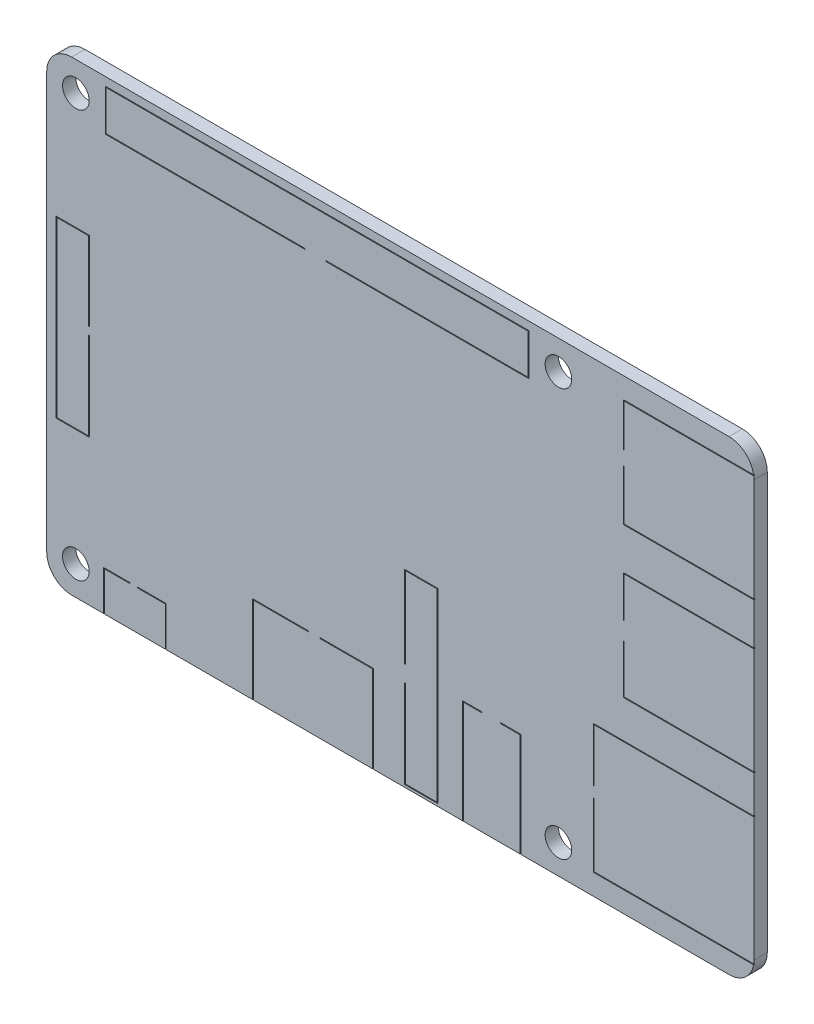
SolidWorks part; units mm, degrees
ref_plane "Front Plane" through (0, 0, 0) normal (0, 0, 1) x (1, 0, 0)
ref_plane "Top Plane" through (0, 0, 0) normal (0, 1, 0) x (1, 0, 0)
ref_plane "Right Plane" through (0, 0, 0) normal (1, 0, 0) x (0, 0, -1)
sketch "Sketch1" plane through (0, 0, 0) normal (0, 0, 1) x (1, 0, 0)
  line L1 (-39.5, -28) -> (39.5, -28)
  line L2 (-42.5, -25) -> (-42.5, 25)
  line L3 (-39.5, 28) -> (39.5, 28)
  line L4 (42.5, -25) -> (42.5, 25)
  line L5 (-42.5, -28) -> (42.5, 28) construction
  line L6 (-42.5, 28) -> (42.5, -28) construction
  arc A0 (-39.5, -28) -> (-42.5, -25) centre (-39.5, -25) cw
  arc A1 (39.5, -28) -> (42.5, -25) centre (39.5, -25) ccw
  arc A2 (39.5, 28) -> (42.5, 25) centre (39.5, 25) cw
  arc A3 (-42.5, 25) -> (-39.5, 28) centre (-39.5, 25) cw
  circle A4 centre (-39, 24.5) radius 1.6
  circle A5 centre (-39, -24.5) radius 1.6
  circle A6 centre (19, 24.5) radius 1.6
  circle A7 centre (19, -24.5) radius 1.6
  point P0 (0, 0)
  dimension "D3" = 3
  dimension "D4" = 3.2
  dimension "D5" = 3.5
  dimension "D6" = 3.5
  dimension "D7" = 58
  dimension "D8" = 58
  dimension "D9" = 49
  dimension "D12" = 49
  dimension "D1" = 85
  dimension "D2" = 56
  dimension "D10" = 24.5
  dimension "D11" = 24.5
extrude "Boss-Extrude1" add sketch "Sketch1" along normal blind 1.6
sketch "Sketch2" plane through (0, 0, 1.6) normal (0, 0, 1) x (1, 0, 0)
  line L1 (-42.5, 25) -> (-42.5, -25) construction
  line L2 (-35.65, -28.6369) -> (-28.15, -28.6369)
  line L3 (-35.65, -28.6369) -> (-35.65, -23.2)
  line L4 (-35.65, -23.2) -> (-32.465, -23.2)
  line L5 (-28.15, -28.6369) -> (-28.15, -23.2)
  line L6 (-35.65, -28.6369) -> (-28.15, -23.2) construction
  line L7 (-35.65, -23.2) -> (-28.15, -28.6369) construction
  line L8 (-39.5, -28) -> (39.5, -28) construction
  line L9 (-17.75, -17.5) -> (-11.0158, -17.5)
  line L10 (-17.75, -17.5) -> (-17.75, -33.1614)
  line L11 (-17.75, -33.1614) -> (-3.25, -33.1614)
  line L12 (-3.25, -17.5) -> (-3.25, -33.1614)
  line L13 (-17.75, -17.5) -> (-3.25, -33.1614) construction
  line L14 (-17.75, -33.1614) -> (-3.25, -17.5) construction
  line L15 (0.5, -5.3) -> (4.5, -5.3)
  line L16 (0.5, -5.3) -> (0.5, -15.174)
  line L17 (0.5, -27.7) -> (4.5, -27.7)
  line L18 (4.5, -5.3) -> (4.5, -27.7)
  line L19 (0.5, -5.3) -> (4.5, -27.7) construction
  line L20 (0.5, -27.7) -> (4.5, -5.3) construction
  line L21 (7.5, -15.5) -> (9.7992, -15.5)
  line L22 (7.5, -15.5) -> (7.5, -31.1614)
  line L23 (7.5, -31.1614) -> (14.5, -31.1614)
  line L24 (14.5, -15.5) -> (14.5, -31.1614)
  line L25 (7.5, -15.5) -> (14.5, -31.1614) construction
  line L26 (7.5, -31.1614) -> (14.5, -15.5) construction
  line L27 (-35.45, 27) -> (15.45, 27)
  line L28 (-35.45, 27) -> (-35.45, 22)
  line L29 (-35.45, 22) -> (-11.4582, 22)
  line L30 (15.45, 27) -> (15.45, 22)
  line L31 (-35.45, 27) -> (15.45, 22) construction
  line L32 (-35.45, 22) -> (15.45, 27) construction
  line L33 (-41.3717, -10.5142) -> (-37.3717, -10.5142)
  line L34 (-41.3717, -10.5142) -> (-41.3717, 10.5142)
  line L35 (-41.3717, 10.5142) -> (-37.3717, 10.5142)
  line L36 (-37.3717, -10.5142) -> (-37.3717, 0.0947)
  line L37 (-41.3717, -10.5142) -> (-37.3717, 10.5142) construction
  line L38 (-41.3717, 10.5142) -> (-37.3717, -10.5142) construction
  line L39 (42.5, -25) -> (42.5, 25) construction
  line L40 (23.2, -25.5) -> (44.7, -25.5)
  line L41 (23.2, -25.5) -> (23.2, -17.75)
  line L42 (23.2, -10) -> (44.7, -10)
  line L43 (44.7, -25.5) -> (44.7, -10)
  line L44 (23.2, -25.5) -> (44.7, -10) construction
  line L45 (23.2, -10) -> (44.7, -25.5) construction
  line L46 (26.8, -5.5) -> (54.0714, -5.5)
  line L47 (26.8, -5.5) -> (26.8, 0.4072)
  line L48 (26.8, 7.5) -> (54.0714, 7.5)
  line L49 (54.0714, -5.5) -> (54.0714, 7.5)
  line L50 (26.8, -5.5) -> (54.0714, 7.5) construction
  line L51 (26.8, 7.5) -> (54.0714, -5.5) construction
  line L52 (26.8, 12.5) -> (57.7137, 12.5)
  line L53 (26.8, 12.5) -> (26.8, 18.6113)
  line L54 (26.8, 25.5) -> (57.7137, 25.5)
  line L55 (57.7137, 12.5) -> (57.7137, 25.5)
  line L56 (26.8, 12.5) -> (57.7137, 25.5) construction
  line L57 (26.8, 25.5) -> (57.7137, 12.5) construction
  line L58 (-35.35, 22.1) -> (-11.4582, 22.1)
  line L59 (15.35, 26.9) -> (15.35, 22.1)
  line L60 (-35.35, 26.9) -> (15.35, 26.9)
  line L61 (-35.35, 26.9) -> (-35.35, 22.1)
  line L62 (-41.2717, 10.4142) -> (-37.4717, 10.4142)
  line L63 (-37.4717, -10.4142) -> (-37.4717, 0.0947)
  line L64 (-41.2717, -10.4142) -> (-37.4717, -10.4142)
  line L65 (-41.2717, -10.4142) -> (-41.2717, 10.4142)
  line L66 (-35.55, -28.5369) -> (-35.55, -23.3)
  line L67 (-35.55, -23.3) -> (-32.465, -23.3)
  line L68 (-28.25, -28.5369) -> (-28.25, -23.3)
  line L69 (-35.55, -28.5369) -> (-28.25, -28.5369)
  line L70 (-17.65, -17.6) -> (-17.65, -33.0614)
  line L71 (-17.65, -33.0614) -> (-3.35, -33.0614)
  line L72 (-3.35, -17.6) -> (-3.35, -33.0614)
  line L73 (-17.65, -17.6) -> (-11.0158, -17.6)
  line L74 (0.6, -5.4) -> (0.6, -15.174)
  line L75 (0.6, -27.6) -> (4.4, -27.6)
  line L76 (4.4, -5.4) -> (4.4, -27.6)
  line L77 (0.6, -5.4) -> (4.4, -5.4)
  line L78 (7.6, -15.6) -> (9.7992, -15.6)
  line L79 (14.4, -15.6) -> (14.4, -31.0614)
  line L80 (7.6, -31.0614) -> (14.4, -31.0614)
  line L81 (7.6, -15.6) -> (7.6, -31.0614)
  line L82 (23.3, -25.4) -> (23.3, -17.75)
  line L83 (23.3, -10.1) -> (44.6, -10.1)
  line L84 (44.6, -25.4) -> (44.6, -10.1)
  line L85 (23.3, -25.4) -> (44.6, -25.4)
  line L86 (26.9, -5.4) -> (53.9714, -5.4)
  line L87 (53.9714, -5.4) -> (53.9714, 7.4)
  line L88 (26.9, 7.4) -> (53.9714, 7.4)
  line L89 (26.9, -5.4) -> (26.9, 0.4072)
  line L90 (26.9, 12.6) -> (57.6137, 12.6)
  line L91 (57.6137, 12.6) -> (57.6137, 25.4)
  line L92 (26.9, 25.4) -> (57.6137, 25.4)
  line L93 (26.9, 12.6) -> (26.9, 18.6113)
  line L94 (-37.4717, 1) -> (-37.4717, 10.4142)
  line L95 (-37.4717, 1) -> (-37.3717, 1)
  line L96 (26.9, 20.2773) -> (26.9, 25.4)
  line L97 (-37.4717, 0.0947) -> (-37.3717, 0.0947)
  line L98 (26.9, 12.6) -> (26.9, 25.4) construction
  line L99 (-37.4717, -10.4142) -> (-37.4717, 10.4142) construction
  line L100 (-37.3717, 1) -> (-37.3717, 10.5142)
  line L101 (-37.3717, -10.5142) -> (-37.3717, 10.5142) construction
  line L102 (26.8, 20.2773) -> (26.9, 20.2773)
  line L103 (26.9, 2.5528) -> (26.9, 7.4)
  line L104 (26.8, 18.6113) -> (26.9, 18.6113)
  line L105 (26.9, -5.4) -> (26.9, 7.4) construction
  line L106 (26.8, 20.2773) -> (26.8, 25.5)
  line L107 (26.8, 12.5) -> (26.8, 25.5) construction
  line L108 (23.2, -16.5) -> (23.3, -16.5)
  line L109 (12.0626, -15.5) -> (14.5, -15.5)
  line L110 (23.2, -17.75) -> (23.3, -17.75)
  line L111 (7.5, -15.5) -> (14.5, -15.5) construction
  line L112 (26.8, 2.5528) -> (26.9, 2.5528)
  line L113 (23.2, -16.5) -> (23.2, -10)
  line L114 (26.8, 0.4072) -> (26.9, 0.4072)
  line L115 (23.2, -25.5) -> (23.2, -10) construction
  line L116 (-8.9067, 22.1) -> (15.35, 22.1)
  line L117 (-32.465, -23.2) -> (-32.465, -23.3)
  line L118 (-35.35, 22.1) -> (15.35, 22.1) construction
  line L119 (-31.5737, -23.2) -> (-31.5737, -23.3)
  line L120 (-31.5737, -23.3) -> (-28.25, -23.3)
  line L121 (-11.0158, -17.5) -> (-11.0158, -17.6)
  line L122 (-35.55, -23.3) -> (-28.25, -23.3) construction
  line L123 (-9.6849, -17.5) -> (-9.6849, -17.6)
  line L124 (0.5, -15.174) -> (0.6, -15.174)
  line L125 (-9.6849, -17.5) -> (-3.25, -17.5)
  line L126 (0.5, -17.125) -> (0.6, -17.125)
  line L127 (-17.75, -17.5) -> (-3.25, -17.5) construction
  line L128 (0.5, -17.125) -> (0.5, -27.7)
  line L129 (9.7992, -15.5) -> (9.7992, -15.6)
  line L130 (0.5, -5.3) -> (0.5, -27.7) construction
  line L131 (12.0626, -15.5) -> (12.0626, -15.6)
  line L132 (26.8, 2.5528) -> (26.8, 7.5)
  line L133 (26.8, -5.5) -> (26.8, 7.5) construction
  line L134 (23.3, -16.5) -> (23.3, -10.1)
  line L135 (23.3, -25.4) -> (23.3, -10.1) construction
  line L136 (12.0626, -15.6) -> (14.4, -15.6)
  line L137 (7.6, -15.6) -> (14.4, -15.6) construction
  line L138 (0.6, -17.125) -> (0.6, -27.6)
  line L139 (0.6, -5.4) -> (0.6, -27.6) construction
  line L140 (-9.6849, -17.6) -> (-3.35, -17.6)
  line L141 (-17.65, -17.6) -> (-3.35, -17.6) construction
  line L142 (-31.5737, -23.2) -> (-28.15, -23.2)
  line L143 (-35.65, -23.2) -> (-28.15, -23.2) construction
  line L145 (-11.4582, 22.1) -> (-11.4582, 22)
  line L147 (-8.9067, 22.1) -> (-8.9067, 22)
  line L148 (-8.9067, 22) -> (15.45, 22)
  line L149 (-35.45, 22) -> (15.45, 22) construction
  circle A0 centre (-39, 24.5) radius 1.6 construction
  point P0 (-31.9, -25.9184)
  point P7 (-10.5, -25.3307)
  point P12 (2.5, -16.5)
  point P17 (11, -23.3307)
  point P22 (-10, 24.5)
  point P29 (-39.3717, 0)
  point P36 (33.95, -17.75)
  point P41 (40.4357, 1)
  point P46 (42.2569, 19)
  dimension "D5" = 29
  dimension "D26" = 0
  dimension "D1" = 10.6
  dimension "D2" = 32
  dimension "D3" = 13
  dimension "D4" = 53.5
  dimension "D6" = 28
  dimension "D7" = 11.5
  dimension "D8" = 10.25
  dimension "D9" = 29
  dimension "D10" = 47
  dimension "D11" = 7.5
  dimension "D12" = 4.8
  dimension "D13" = 14.5
  dimension "D14" = 10.5
  dimension "D15" = 4
  dimension "D16" = 22.7
  dimension "D17" = 7
  dimension "D18" = 12.5
  dimension "D19" = 15.5
  dimension "D20" = 19.3
  dimension "D21" = 21.5
  dimension "D22" = 13
  dimension "D23" = 13
  dimension "D24" = 15.7
  dimension "D25" = 15.7
  dimension "D27" = 5
  dimension "D28" = 50.9
  dimension "D29" = 4
  dimension "D30" = 0.1
extrude "Cut-Extrude1" cut sketch "Sketch2" against normal blind 0.1
